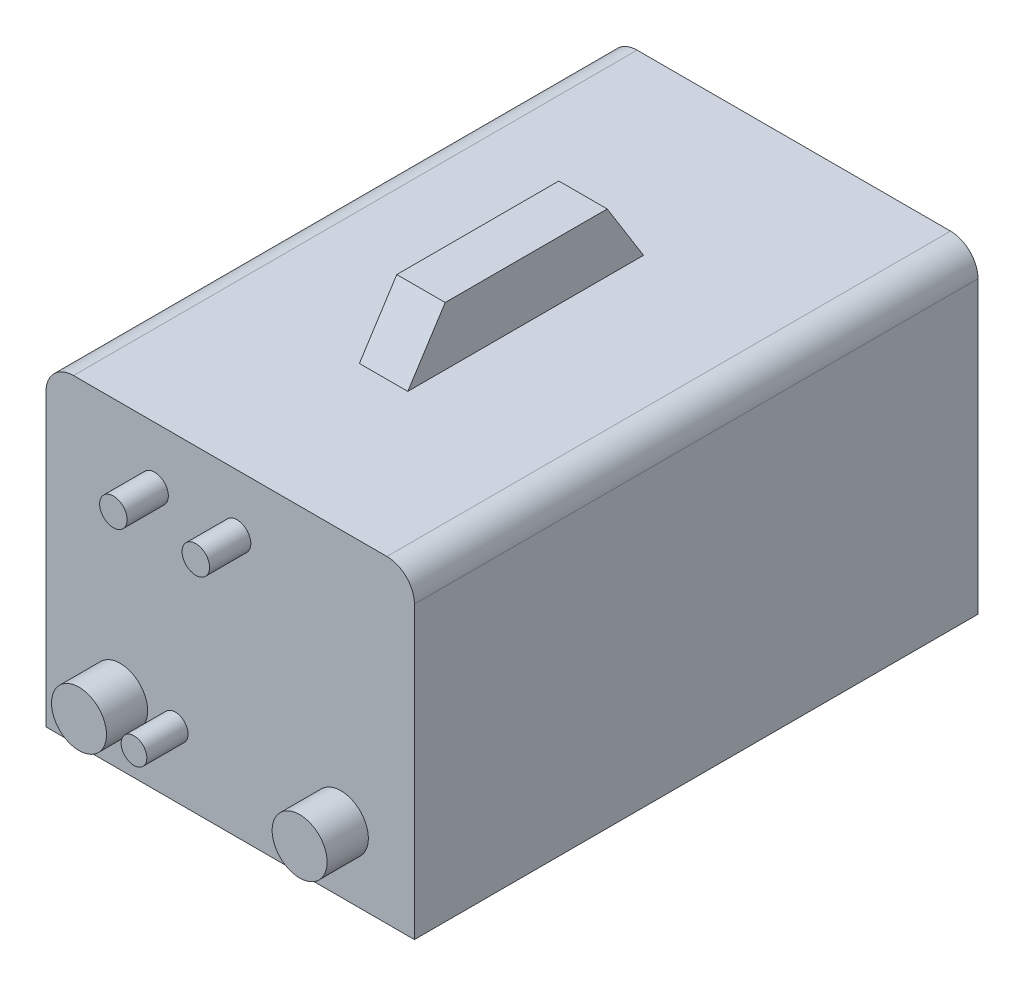
SolidWorks part; units mm, degrees
ref_plane "Спереди" through (0, 0, 0) normal (0, 0, 1) x (1, 0, 0)
ref_plane "Сверху" through (0, 0, 0) normal (0, 1, 0) x (1, 0, 0)
ref_plane "Справа" through (0, 0, 0) normal (1, 0, 0) x (0, 0, -1)
sketch "Эскиз2" plane through (0, 0, 0) normal (0, 0, 1) x (1, 0, 0)
  line L0 (-134, 0) -> (134, 0)
  line L1 (134, 0) -> (134, 211.3834)
  line L2 (114, 231.3834) -> (17.6138, 231.3834)
  line L3 (17.6138, 231.3834) -> (17.6138, 273.7955)
  line L8 (17.6138, 273.7955) -> (-17.6138, 273.7955)
  line L9 (0, 382.3728) -> (0, -59.8962) construction
  line L10 (-114, 231.3834) -> (-17.6138, 231.3834)
  line L11 (-134, 0) -> (-134, 211.3834)
  line L12 (-17.6138, 231.3834) -> (-17.6138, 273.7955)
  arc A0 (-114, 231.3834) -> (-134, 211.3834) centre (-114, 211.3834) ccw
  arc A1 (134, 211.3834) -> (114, 231.3834) centre (114, 211.3834) ccw
  point P9 (0, 0)
  point P13 (0, 273.7955)
  point P15 (-134, 231.3834)
  point P18 (134, 231.3834)
  point P19 (0, 0)
  point P20 (0, 0)
  point P21 (0, 0)
  point P22 (0, 0)
  point P23 (0, 0)
  point P24 (70.4552, 300.4462)
  point P25 (108.3249, 259.9344)
  point P26 (53.2818, 264.7782)
  point P27 (17.6138, 298.6848)
  point P28 (17.6138, 271.3834)
  point P29 (0, 0)
  point P30 (0, 0)
  dimension "D1" = 20
extrude "Бобышка-Вытянуть1" add sketch "Эскиз2" along normal blind 410
sketch "Эскиз3" plane through (0, 0, 0) normal (1, 0, 0) x (0, 0, -1)
  line L0 (-271.2064, 273.7955) -> (-298.4112, 231.3834)
  line L2 (-126.945, 231.3834) -> (0, 231.3834)
  line L3 (-298.4112, 231.3834) -> (-410.4939, 231.3834)
  line L4 (-410.4939, 231.3834) -> (-410.4939, 334.8564)
  line L5 (-410.4939, 334.8564) -> (0, 334.8564)
  line L6 (0, 231.3834) -> (0, 334.8564)
  line L12 (-271.2064, 273.7955) -> (-153.3384, 273.7955)
  line L14 (-410, 231.3834) -> (0, 231.3834) construction
  line L15 (-153.3384, 273.7955) -> (-126.945, 231.3834)
  line L16 (-410, 273.7955) -> (0, 273.7955) construction
  point P9 (-159.703, 344.7334)
  point P11 (-114.5545, 271.3834)
  point P12 (-395.2856, 231.3834)
  point P15 (-156.23, 273.7955)
  point P18 (-368.0807, 273.7955)
  point P19 (-150.1045, 273.7955)
extrude "Вырез-Вытянуть1" cut sketch "Эскиз3" against normal mid plane 330
sketch "Эскиз4" plane through (0, 0, 410) normal (0, 0, 1) x (1, 0, 0)
  circle A0 centre (-80, 47.0693) radius 20
  circle A1 centre (-40, 47.0693) radius 9.341
  circle A2 centre (80.5093, 47.0693) radius 20
  circle A4 centre (-55, 190) radius 10
  circle A5 centre (5, 190) radius 10
  point P8 (0, 0)
  dimension "D1" = 2
sketch "Эскиз5" plane through (0, 0, 0) normal (0, 0, -1) x (-1, 0, 0)
  circle A0 centre (-12.3022, 29.9341) radius 8.2549
  circle A1 centre (-73.8134, 29.9341) radius 9.2267
extrude "Бобышка-Вытянуть2" add sketch "Эскиз4" along normal blind 30
extrude "Бобышка-Вытянуть3" add sketch "Эскиз5" along normal blind 30
